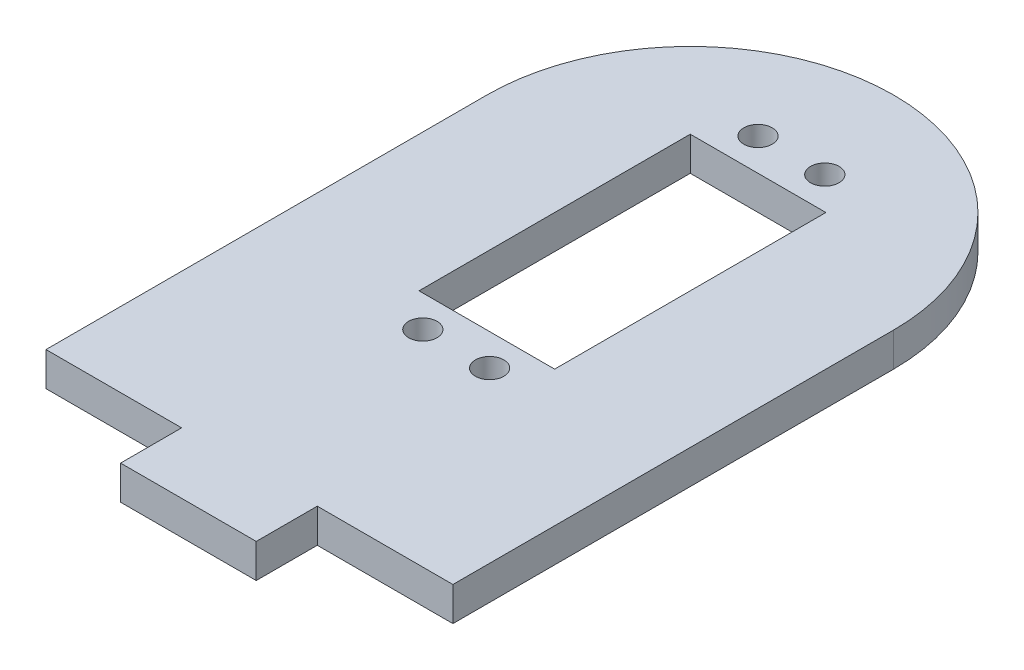
SolidWorks part; units mm, degrees
ref_plane "Front Plane" through (0, 0, 0) normal (0, 0, 1) x (1, 0, 0)
ref_plane "Top Plane" through (0, 0, 0) normal (0, 1, 0) x (1, 0, 0)
ref_plane "Right Plane" through (0, 0, 0) normal (1, 0, 0) x (0, 0, -1)
sketch "Sketch1" plane through (0, 0, 0) normal (0, 1, 0) x (1, 0, 0)
  line L0 (0, 32.5) -> (0, -32.5) construction
  line L1 (-30, -32.5) -> (30, -32.5)
  line L2 (-30, -32.5) -> (-30, 32.5)
  line L3 (-30, 32.5) -> (30, 32.5)
  line L4 (30, -32.5) -> (30, 32.5)
  line L5 (-30, -32.5) -> (30, 32.5) construction
  line L6 (-30, 32.5) -> (30, -32.5) construction
  line L7 (-30, 0) -> (30, 0) construction
  line L8 (-10, -32.5) -> (-10, -41.5)
  line L9 (-10, -41.5) -> (10, -41.5)
  line L10 (10, -41.5) -> (10, -32.5)
  line L11 (10, -32.5) -> (-10, -32.5)
  arc A0 (30, 32.5) -> (-30, 32.5) centre (0, 32.5) ccw
  point P0 (0, 0)
  dimension "D6" = 30
  dimension "D1" = 60
  dimension "D2" = 65
  dimension "D3" = 20
  dimension "D4" = 20
  dimension "D5" = 9
extrude "Boss-Extrude1" add sketch "Sketch1" along normal blind 5 contours L1 L4 L3 L2 | L9 L10 L1 L8 | L3 A0
sketch "Sketch2" plane through (0, 5, 0) normal (0, 1, 0) x (1, 0, 0)
  line L0 (0, 62.5) -> (0, -41.5) construction
  line L7 (-10, 42.5) -> (10, 42.5)
  line L8 (-10, -41.5) -> (10, -41.5) construction
  line L9 (-30, 0) -> (30, 0) construction
  line L10 (-30, -32.5) -> (-30, 32.5) construction
  line L11 (30, -32.5) -> (30, 32.5) construction
  line L12 (-10, 42.5) -> (-10, 2.5)
  line L13 (-10, 2.5) -> (10, 2.5)
  line L14 (10, 42.5) -> (10, 2.5)
  line L15 (-10, 42.5) -> (10, 2.5) construction
  line L16 (-10, 2.5) -> (10, 42.5) construction
  arc A1 (30, 32.5) -> (-30, 32.5) centre (0, 32.5) ccw construction
  arc A2 (30, 32.5) -> (-30, 32.5) centre (0, 32.5) ccw construction
  point P3 (0, 62.5)
  point P4 (2.7426, 17.6633)
  point P5 (0, 22.5)
  dimension "D1" = 20
  dimension "D2" = 40
  dimension "D3" = 10
extrude "Cut-Extrude1" cut sketch "Sketch2" against normal through all
sketch "Sketch3" plane through (0, 0, 0) normal (0, -1, 0) x (1, 0, 0)
  circle A0 centre (-4.775, 2.1611) radius 2.1
  circle A1 centre (5.075, 2.1611) radius 2.1
  circle A2 centre (5.075, -47.2611) radius 2.1
  circle A3 centre (-4.775, -47.2611) radius 2.1
  dimension "D1" = 4.2
  dimension "D2" = 4.2
  dimension "D3" = 4.2
  dimension "D4" = 4.2
extrude "Cut-Extrude2" cut sketch "Sketch3" against normal through all and the other way through all
